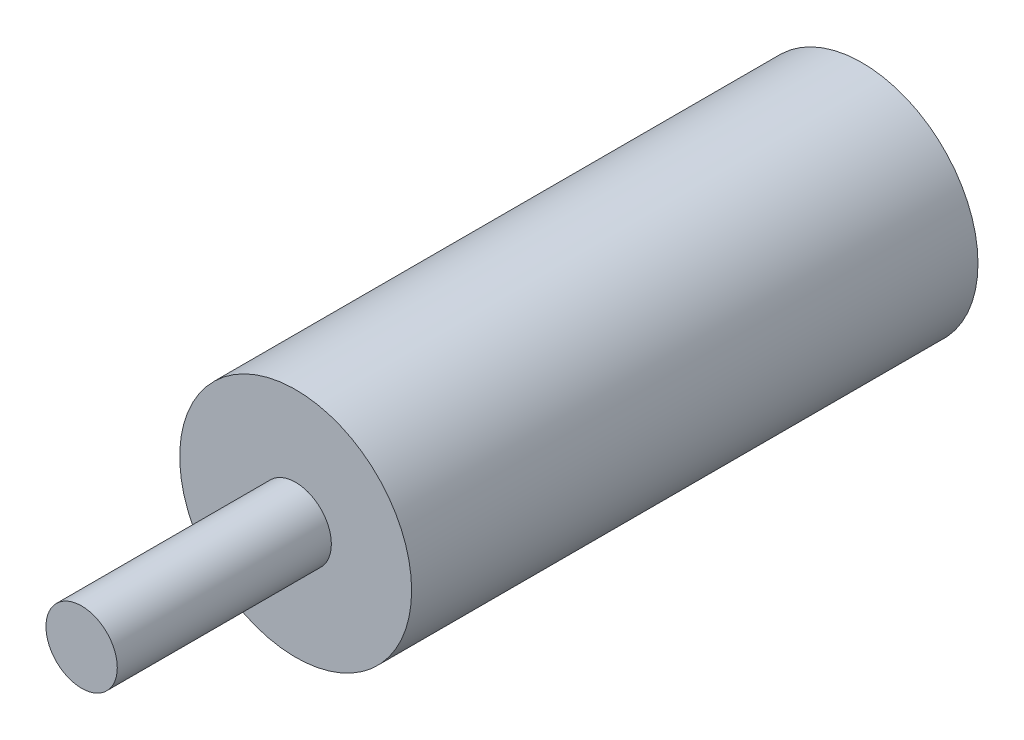
SolidWorks part; units mm, degrees
ref_plane "Front Plane" through (0, 0, 0) normal (0, 0, 1) x (1, 0, 0)
ref_plane "Top Plane" through (0, 0, 0) normal (0, 1, 0) x (1, 0, 0)
ref_plane "Right Plane" through (0, 0, 0) normal (1, 0, 0) x (0, 0, -1)
ref_plane "Plane1"
sketch "Sketch1" plane through (0, 0, 0) normal (0, 0, 1) x (1, 0, 0)
  circle A0 centre (0, 0) radius 26
  circle A1 centre (0, 0) radius 8
  dimension "D1" = 52
  dimension "D2" = 16
extrude "Extrusion1" add sketch "Sketch1" along normal blind 127 contours A0 A1
ref_plane "Plane2"
sketch "Sketch2" plane through (0, 0, 0) normal (0, 0, 1) x (1, 0, 0)
  circle A0 centre (0, 0) radius 8
  dimension "D1" = 16
extrude "Extrusion2" add sketch "Sketch2" along normal blind 175
